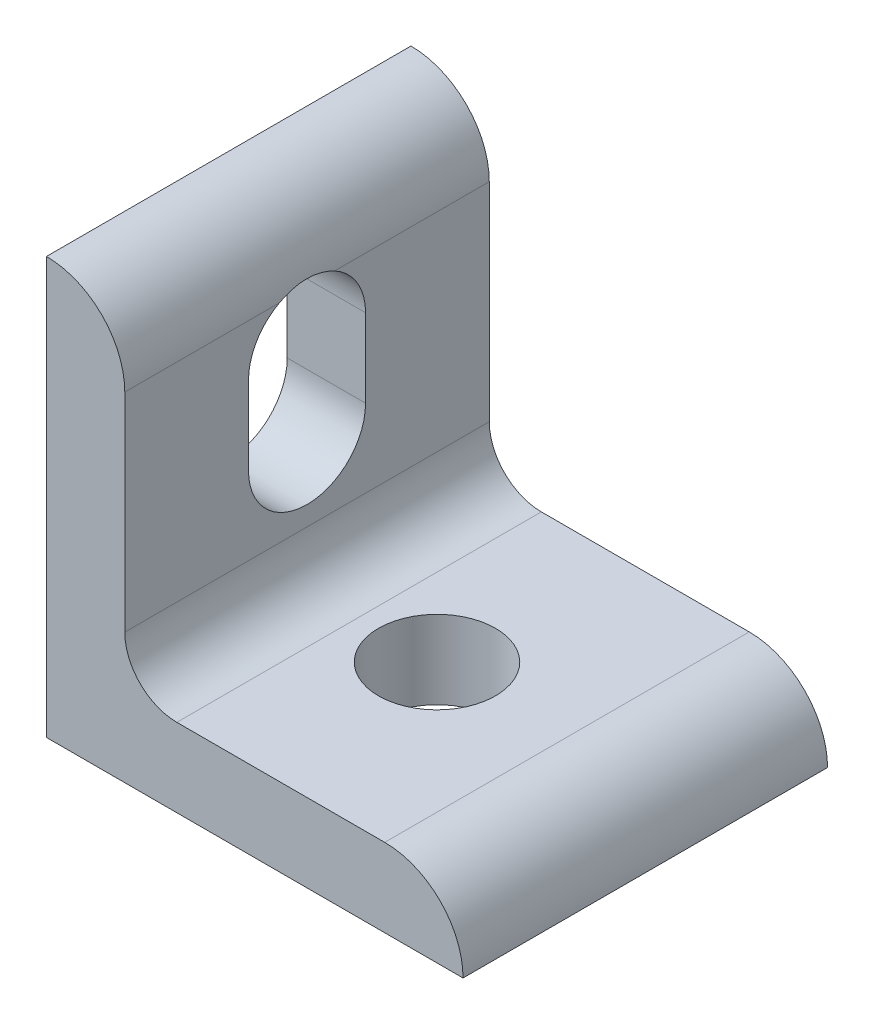
SolidWorks part; units mm, degrees
ref_plane "Front Plane" through (0, 0, 0) normal (0, 0, 1) x (1, 0, 0)
ref_plane "Top Plane" through (0, 0, 0) normal (0, 1, 0) x (1, 0, 0)
ref_plane "Right Plane" through (0, 0, 0) normal (1, 0, 0) x (0, 0, -1)
sketch "Sketch1" plane through (0, 0, 0) normal (0, 0, 1) x (1, 0, 0)
  line L0 (12.7, -12.7) -> (-12.7, -12.7) construction
  line L1 (12.7, -12.7) -> (12.7, -7.9248) construction
  line L2 (-12.7, -12.7) -> (-12.7, 12.7) construction
  point P0 (-12.7, 0)
  point P3 (0, -12.7)
  dimension "Length" = 25.4
  dimension "Thickness" = 4.7752
sketch "Sketch2" plane through (0, 0, 0) normal (1, 0, 0) x (0, 0, -1)
  line L0 (-11.1125, -12.7) -> (11.1125, -12.7) construction
  line L2 (0, 4.7752) -> (0, 0) construction
  line L3 (0, -12.7) -> (0, 12.7) construction
  line L4 (3.5687, 4.7752) -> (-3.5687, 4.7752) construction
  point P4 (0, -12.7)
  point P12 (0, 4.7752)
  dimension "Width" = 22.225
  dimension "Bottom to Slot" = 12.7
  dimension "Slot Width" = 4.7752
  dimension "Slot Dia" = 7.1374
sketch "Sketch3" plane through (0, 0, 0) normal (0, 1, 0) x (1, 0, 0)
  line L0 (-3.5687, 0) -> (3.5687, 0) construction
  line L1 (12.7, 0) -> (-12.7, 0) construction
  point P5 (0, 0)
  dimension "Hole Dia" = 7.1374
sketch "Sketch4" plane through (0, 0, 0) normal (0, 0, 1) x (1, 0, 0)
  line L0 (-12.7, 12.7) -> (-12.7, -12.7)
  line L1 (-12.7, -12.7) -> (12.7, -12.7)
  line L2 (7.9248, -7.9248) -> (-4.7498, -7.9248)
  line L3 (-7.9248, -4.7498) -> (-7.9248, 7.9248)
  arc A0 (-4.7498, -7.9248) -> (-7.9248, -4.7498) centre (-4.7498, -4.7498) cw
  arc A1 (7.9248, -7.9248) -> (12.7, -12.7) centre (7.9248, -12.7) cw
  arc A2 (-7.9248, 7.9248) -> (-12.7, 12.7) centre (-12.7, 7.9248) ccw
  dimension "D1" = 3.175
extrude "Boss-Extrude1" add sketch "Sketch4" against normal up to vertex (11.1125 mm away) and the other way up to vertex (11.1125 mm away) up to point (0, -12.7, -11.1125) other way up to point (0, -12.7, 11.1125)
sketch "Sketch5" plane through (-7.9248, 0, 0) normal (1, 0, 0) x (0, 0, -1)
  line L0 (0, 4.7752) -> (0, 0) construction
  line L1 (3.5687, 4.7752) -> (-3.5687, 4.7752) construction
  line L2 (3.5687, 4.7752) -> (3.5687, 0)
  line L3 (-3.5687, 4.7752) -> (-3.5687, 0)
  arc A0 (3.5687, 4.7752) -> (-3.5687, 4.7752) centre (0, 4.7752) ccw
  arc A1 (-3.5687, 0) -> (3.5687, 0) centre (0, 0) ccw
  point P5 (0, 2.3876)
extrude "Cut-Extrude1" cut sketch "Sketch5" against normal through all both and the other way through all
sketch "Sketch6" plane through (0, -7.9248, 0) normal (0, 1, 0) x (1, 0, 0)
  line L0 (12.7, 0) -> (-12.7, 0) construction
  circle A0 centre (0, 0) radius 3.5687
extrude "Cut-Extrude2" cut sketch "Sketch6" against normal through all
